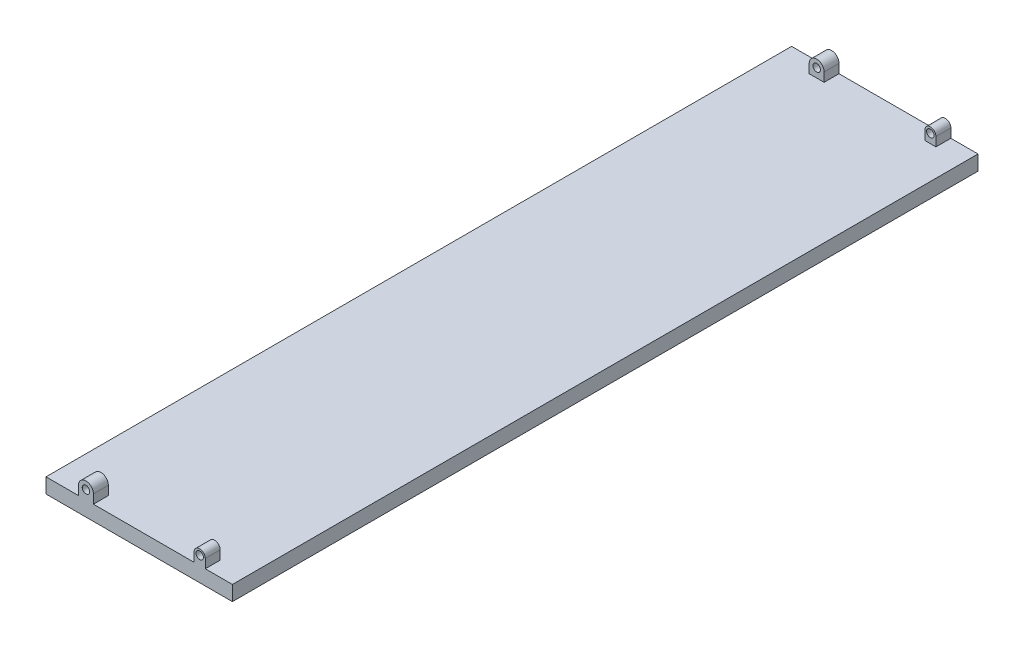
SolidWorks part; units mm, degrees
material "Alloy Steel"
ref_plane "Front Plane" through (0, 0, 0) normal (0, 0, 1) x (1, 0, 0)
ref_plane "Top Plane" through (0, 0, 0) normal (0, 1, 0) x (1, 0, 0)
ref_plane "Right Plane" through (0, 0, 0) normal (1, 0, 0) x (0, 0, -1)
sketch "Sketch2" plane through (0, 0, 0) normal (0, 0, 1) x (1, 0, 0)
  line L1 (-125, -10) -> (125, -10)
  line L2 (-125, -10) -> (-125, 10)
  line L3 (-125, 10) -> (125, 10)
  line L4 (125, -10) -> (125, 10)
  line L5 (-125, -10) -> (125, 10) construction
  line L6 (-125, 10) -> (125, -10) construction
  point P0 (0, 0)
  dimension "D1" = 20
  dimension "D2" = 250
extrude "Boss-Extrude1" add sketch "Sketch2" against normal blind 1000
sketch "Sketch3" plane through (0, 0, 0) normal (0, 0, 1) x (1, 0, 0)
  line L0 (88.6, 10) -> (88.6, 22)
  line L1 (125, 10) -> (-125, 10) construction
  line L2 (73.6, 22) -> (73.6, 10)
  line L3 (73.6, 10) -> (88.6, 10)
  line L4 (125, -10) -> (125, 10) construction
  arc A0 (88.6, 22) -> (73.6, 22) centre (81.1, 22) ccw
  dimension "D1" = 12
  dimension "D2" = 36.4
  dimension "D3" = 15
extrude "Boss-Extrude2" add sketch "Sketch3" against normal blind 20
sketch "Sketch4" plane through (0, 0, 0) normal (0, 0, 1) x (1, 0, 0)
  line L0 (-81.4, 10) -> (-81.4, 22)
  line L1 (73.6, 10) -> (-125, 10) construction
  line L2 (-61.4, 22) -> (-61.4, 10)
  line L3 (-61.4, 10) -> (-81.4, 10)
  line L4 (88.6, 10) -> (88.6, 22) construction
  arc A0 (-81.4, 22) -> (-61.4, 22) centre (-71.4, 22) cw
  dimension "D1" = 170
  dimension "D2" = 20
  dimension "D3" = 12
extrude "Boss-Extrude3" add sketch "Sketch4" against normal blind 20
hole_wizard "Ø10.0mm Dowel Hole1" positions "Sketch5" profile "Sketch6" hole size "Ø10.0" standard "ANSI Metric" end condition through all
sketch "Sketch5" plane through (0, 0, 0) normal (0, 0, 1) x (1, 0, 0)
  point P0 (-71.4, 22)
  point P3 (81.1, 22)
sketch "Sketch6" plane through (-71.4, 22, 0) normal (1, 0, 0) x (0, -1, 0)
  line L0 (0, 0) -> (0, 1000)
  line L1 (0, 1000) -> (5, 1000)
  line L2 (5, 1000) -> (5, 0.025)
  line L3 (5, 0.025) -> (5.025, 0)
  line L5 (5.025, 0) -> (0, 0)
  line L6 (-5, 0.025) -> (-5.025, 0) construction
  line L11 (0, -6.35) -> (0, 107.95) construction
  dimension "Thru Hole Dia." = 10
  dimension "Thru Hole Depth" = 1000
  dimension "Near C'Sink Dia." = 10.05
  dimension "Near C'Sink Angle" = 90
ref_plane "Plane1" through (0, 0, -500) normal (0, 0, 1) x (1, 0, 0)
mirror "Mirror1" about plane through (0, 0, -500) normal (0, 0, 1) of "Boss-Extrude2", "Ø10.0mm Dowel Hole1", "Boss-Extrude3"
